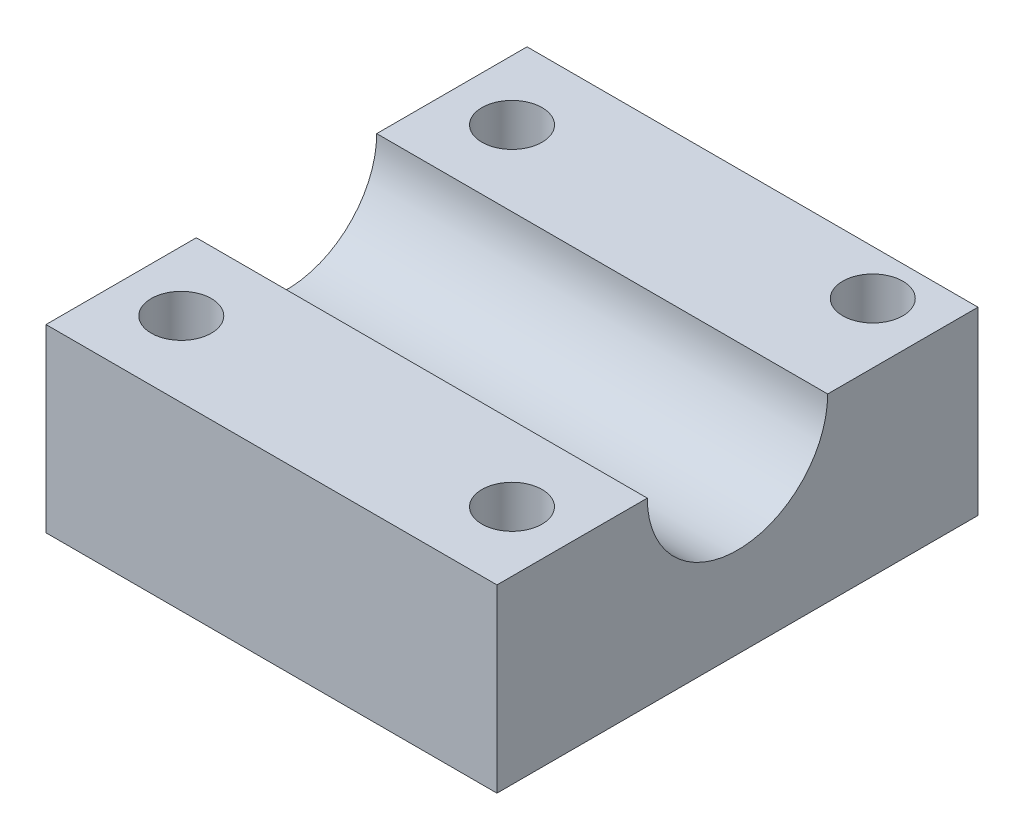
SolidWorks part; units mm, degrees
ref_plane "Front Plane" through (0, 0, 0) normal (0, 0, 1) x (1, 0, 0)
ref_plane "Top Plane" through (0, 0, 0) normal (0, 1, 0) x (1, 0, 0)
ref_plane "Right Plane" through (0, 0, 0) normal (1, 0, 0) x (0, 0, -1)
sketch "Sketch1" plane through (0, 0, 0) normal (1, 0, 0) x (0, 0, -1)
  line L0 (0, 0) -> (0, 12)
  line L1 (0, 12) -> (10, 12)
  line L2 (0, 0) -> (32, 0)
  line L3 (16, 6) -> (16, -29.5365) construction
  line L4 (32, 12) -> (22, 12)
  line L5 (32, 0) -> (32, 12)
  arc A0 (10, 12) -> (22, 12) centre (16, 12) ccw
  point P10 (16, 0)
  dimension "D3" = 6
  dimension "D4" = 12
  dimension "D1" = 12
  dimension "D2" = 10
extrude "Boss-Extrude1" add sketch "Sketch1" along normal blind 30
sketch "Sketch2" plane through (0, 12, 0) normal (0, 1, 0) x (1, 0, 0)
  line L0 (30, 32) -> (0, 32) construction
  line L1 (0, 32) -> (0, 22) construction
  line L2 (30, 32) -> (30, 22) construction
  circle A0 centre (4, 27) radius 2
  circle A1 centre (26, 29) radius 2
  circle A2 centre (4, 5) radius 2
  circle A3 centre (26, 5) radius 2
  dimension "D1" = 5
  dimension "D2" = 4
  dimension "D3" = 4
extrude "Cut-Extrude1" cut sketch "Sketch2" against normal through all
